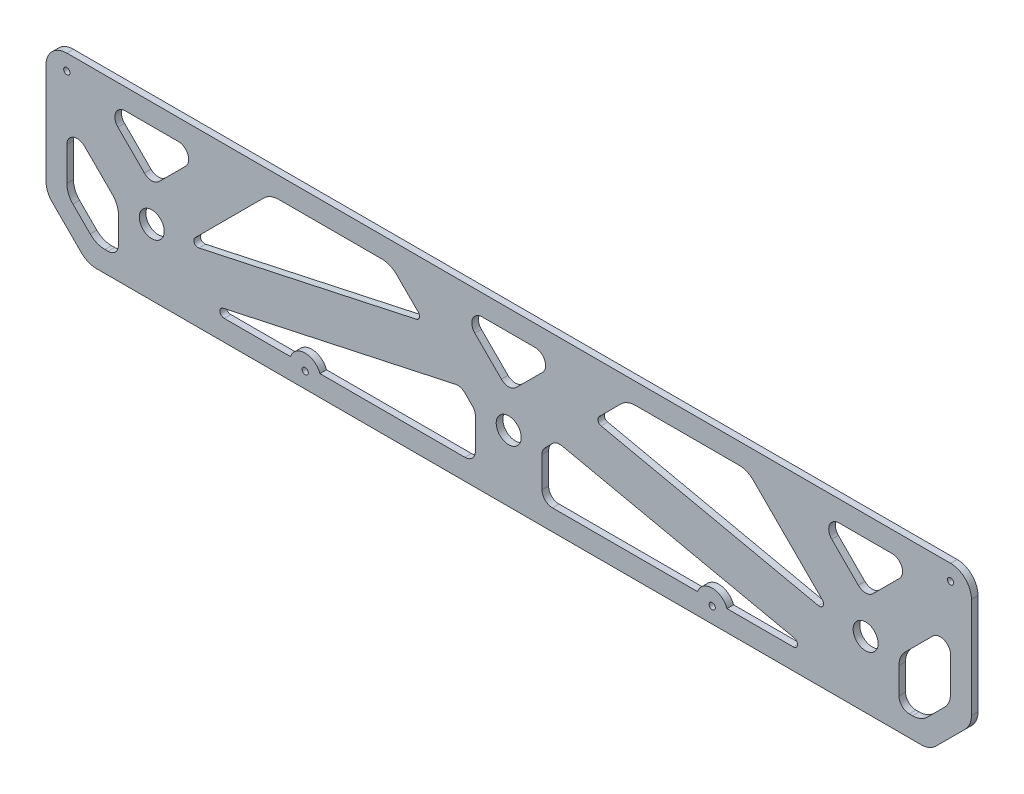
SolidWorks part; units mm, degrees
ref_plane "Front Plane" through (0, 0, 0) normal (0, 0, 1) x (1, 0, 0)
ref_plane "Top Plane" through (0, 0, 0) normal (0, 1, 0) x (1, 0, 0)
ref_plane "Right Plane" through (0, 0, 0) normal (1, 0, 0) x (0, 0, -1)
sketch "Sketch1" plane through (0, 0, 0) normal (0, 0, 1) x (1, 0, 0)
  line L0 (2.9289, 17.0711) -> (17.0711, 2.9289)
  line L1 (24.1421, 0) -> (420.3579, 0)
  line L2 (0, 24.1421) -> (0, 72.55)
  line L3 (10, 82.55) -> (434.5, 82.55)
  line L4 (444.5, 24.1421) -> (444.5, 72.55)
  line L5 (427.4289, 2.9289) -> (441.5711, 17.0711)
  line L6 (10, 28.2843) -> (10, 56.5504)
  line L7 (25.9996, 72.55) -> (75.6004, 72.55)
  line L8 (434.5, 28.2843) -> (434.5, 62.55)
  line L9 (423.2868, 12.9289) -> (431.5711, 21.2132)
  line L10 (28.2843, 10) -> (34.8004, 10)
  line L11 (12.9289, 21.2132) -> (21.2132, 12.9289)
  line L12 (222.25, 82.55) -> (222.25, 25.75) construction
  line L13 (0, 82.55) -> (444.5, 82.55) construction
  line L14 (444.5, 20) -> (444.5, 82.55) construction
  line L15 (0, 20) -> (0, 82.55) construction
  line L16 (10, 72.55) -> (434.5, 72.55) construction
  line L17 (434.5, 24.1421) -> (434.5, 72.55) construction
  line L18 (10, 24.1421) -> (10, 72.55) construction
  line L19 (420.3579, 10) -> (434.5, 24.1421) construction
  line L20 (24.1421, 10) -> (420.3579, 10) construction
  line L21 (10, 24.1421) -> (24.1421, 10) construction
  line L22 (0, 20) -> (20, 0) construction
  line L23 (20, 0) -> (424.5, 0) construction
  line L24 (424.5, 0) -> (444.5, 20) construction
  line L25 (34.8004, 31.75) -> (34.8004, 10)
  line L26 (409.6996, 10) -> (416.2157, 10)
  line L27 (206.25, 31.75) -> (206.25, 10)
  line L28 (238.25, 31.75) -> (238.25, 10)
  line L29 (66.7996, 10) -> (117.4168, 10)
  line L30 (409.6996, 31.75) -> (409.6996, 10)
  line L31 (222.25, 47.75) -> (197.45, 72.55)
  line L32 (206.25, 31.75) -> (199.3315, 38.6685)
  line L33 (222.25, 47.75) -> (247.05, 72.55)
  line L34 (238.25, 31.75) -> (245.1685, 38.6685)
  line L35 (197.45, 72.55) -> (247.05, 72.55)
  line L36 (279.05, 72.55) -> (336.9004, 72.55)
  line L37 (66.7996, 31.75) -> (107.5996, 72.55)
  line L38 (34.8004, 31.75) -> (10, 56.5504)
  line L39 (50.8, 47.7496) -> (25.9996, 72.55)
  line L40 (50.8, 47.7496) -> (75.6004, 72.55)
  line L41 (131.5589, 10) -> (206.25, 10)
  line L42 (409.6996, 31.75) -> (434.5, 56.5504)
  line L43 (393.7, 47.7496) -> (418.5004, 72.55)
  line L44 (393.7, 47.7496) -> (368.8996, 72.55)
  line L45 (377.7004, 31.75) -> (336.9004, 72.55)
  line L46 (66.7996, 31.75) -> (181.4496, 56.5504)
  line L47 (66.7996, 10) -> (199.3315, 38.6685)
  line L48 (377.7004, 10) -> (245.1685, 38.6685)
  line L49 (377.7004, 31.75) -> (263.0504, 56.5504)
  line L50 (181.4496, 56.5504) -> (165.45, 72.55)
  line L51 (263.0504, 56.5504) -> (279.05, 72.55)
  line L52 (238.25, 10) -> (312.9411, 10)
  line L53 (107.5996, 72.55) -> (165.45, 72.55)
  line L54 (368.8996, 72.55) -> (418.5004, 72.55)
  line L55 (327.0832, 10) -> (377.7004, 10)
  circle A0 centre (50.8, 31.75) radius 5.9996
  circle A1 centre (393.7, 31.75) radius 5.9996
  circle A2 centre (222.25, 31.75) radius 6
  arc A3 (434.5, 82.55) -> (444.5, 72.55) centre (434.5, 72.55) cw
  arc A4 (0, 72.55) -> (10, 82.55) centre (10, 72.55) cw
  arc A7 (434.5, 28.2843) -> (431.5711, 21.2132) centre (424.5, 28.2843) cw
  arc A8 (423.2868, 12.9289) -> (416.2157, 10) centre (416.2157, 20) cw
  arc A9 (10, 28.2843) -> (12.9289, 21.2132) centre (20, 28.2843) ccw
  arc A10 (28.2843, 10) -> (21.2132, 12.9289) centre (28.2843, 20) cw
  arc A11 (17.0711, 2.9289) -> (24.1421, 0) centre (24.1421, 10) ccw
  arc A12 (2.9289, 17.0711) -> (0, 24.1421) centre (10, 24.1421) cw
  arc A13 (441.5711, 17.0711) -> (444.5, 24.1421) centre (434.5, 24.1421) ccw
  arc A14 (427.4289, 2.9289) -> (420.3579, 0) centre (420.3579, 10) cw
  circle A18 centre (10, 75.05) radius 1.5
  circle A19 centre (434.5, 75.05) radius 1.5
  circle A21 centre (124.4878, 7.5) radius 1.5
  arc A22 (131.5589, 10) -> (117.4168, 10) centre (124.4878, 7.5) ccw
  arc A23 (312.9411, 10) -> (327.0832, 10) centre (320.0122, 7.5) cw
  circle A24 centre (320.0122, 7.5) radius 1.5
  point P0 (0, 0)
  point P3 (444.5, 0)
  point P15 (24.1421, 24.1421)
  point P16 (17.0711, 17.0711)
  point P17 (427.4289, 17.0711)
  point P18 (420.3579, 24.1421)
  point P35 (0, 0)
  point P54 (20, 0)
  point P75 (124.4878, 0)
  point P76 (222.25, 10)
  point P77 (222.25, 10)
  point P78 (320.0122, 0)
  point P79 (222.25, 10)
  point P104 (320.0122, 7.5)
  point P106 (0, 0)
  point P110 (0, 0)
  point P111 (0, 0)
  point P112 (0, 0)
  dimension "D4" = 31.75
  dimension "D6" = 10
  dimension "D1" = 10
  dimension "D9" = 10
  dimension "D12" = 7.5
  dimension "D8" = 7.5
  dimension "D2" = 444.5
  dimension "D5" = 50.8
  dimension "D3" = 10
extrude "Boss-Extrude1" add sketch "Sketch1" along normal blind 3.175 contours A14 L5 A13 L4 A3 L3 A4 L2 A12 L0 A11 L1 L41 A22 L29 L47 L32 L27 A19 A18 A2 L44 L54 L43 L37 L53 L50 L46 L49 L51 L36 L45 L31 L35 L33 L40 L39 L7 A0 A1
fillet "Fillet1" radius 10 6 edges at (279.05, 72.55, 1.5875) (165.45, 72.55, 1.5875) (409.6996, 31.75, 1.5875) (336.9004, 72.55, 1.5875) (34.8004, 31.75, 1.5875) (107.5996, 72.55, 1.5875)
fillet "Fillet2" radius 5 8 edges at (199.3315, 38.6685, 1.5875) (245.1685, 38.6685, 1.5875) (238.25, 31.75, 1.5875) (206.25, 31.75, 1.5875) (409.6996, 10, 1.5875) (206.25, 10, 1.5875) (238.25, 10, 1.5875) (34.8004, 10, 1.5875)
fillet "Fillet3" radius 5 3 edges at (197.45, 72.55, 1.5875) (247.05, 72.55, 1.5875) (222.25, 47.75, 1.5875)
fillet "Fillet4" radius 5 8 edges at (434.5, 56.5504, 1.5875) (393.7, 47.7496, 1.5875) (418.5004, 72.55, 1.5875) (368.8996, 72.55, 1.5875) (10, 56.5504, 1.5875) (25.9996, 72.55, 1.5875) (75.6004, 72.55, 1.5875) (50.8, 47.7496, 1.5875)
fillet "Fillet5" radius 2 6 edges at (263.0504, 56.5504, 1.5875) (181.4496, 56.5504, 1.5875) (377.7004, 31.75, 1.5875) (377.7004, 10, 1.5875) (66.7996, 10, 1.5875) (66.7996, 31.75, 1.5875)
